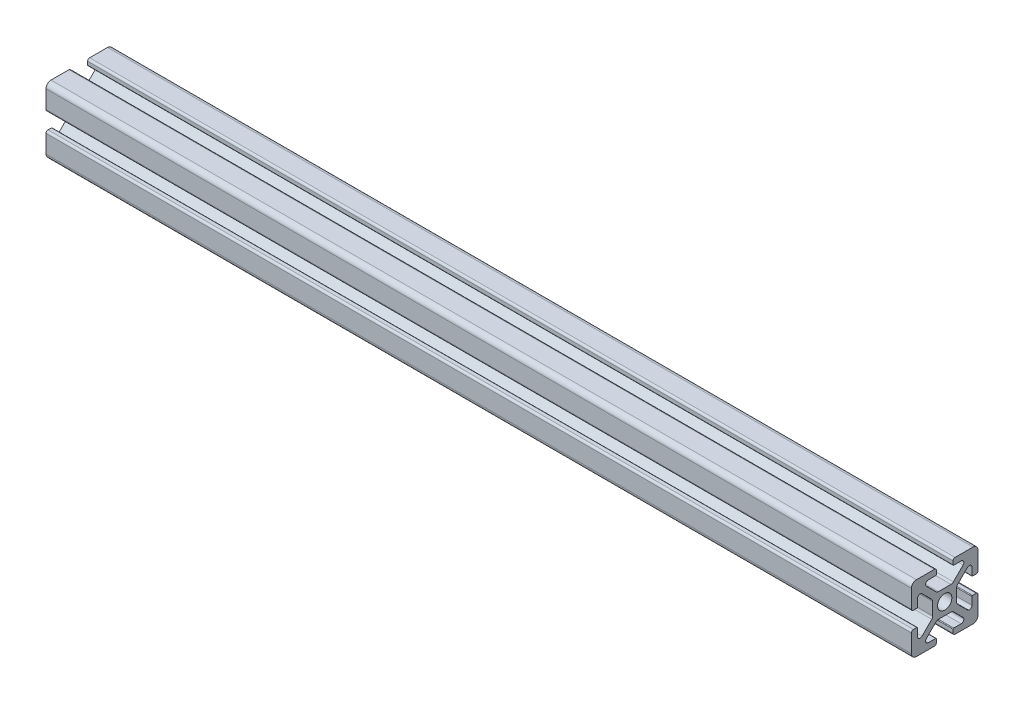
SolidWorks part; units mm, degrees
ref_plane "Front Plane" through (0, 0, 0) normal (0, 0, 1) x (1, 0, 0)
ref_plane "Top Plane" through (0, 0, 0) normal (0, 1, 0) x (1, 0, 0)
ref_plane "Right Plane" through (0, 0, 0) normal (1, 0, 0) x (0, 0, -1)
sketch "Sketch1" plane through (0, 0, 0) normal (1, 0, 0) x (0, 0, -1)
  line L0 (0, -10) -> (0, 10) construction
  line L1 (10, -10) -> (-10, -10)
  line L2 (10, -10) -> (10, 10)
  line L3 (10, 10) -> (0, 10)
  line L4 (-10, -10) -> (-10, 10)
  line L5 (10, -10) -> (-10, 10) construction
  line L6 (10, 10) -> (-10, -10) construction
  line L7 (10, 0) -> (-10, 0) construction
  line L8 (-2.5, 9.4) -> (-2.5, 8.3731)
  line L9 (-2.7, 8.1731) -> (-4.95, 8.1731)
  line L10 (-5.5157, 6.8075) -> (-2.6011, 3.8929)
  line L11 (-1.894, 3.6) -> (0, 3.6)
  line L12 (-5.3502, 4.0584) -> (-4.0584, 5.3502) construction
  line L13 (-3.825, 8.1731) -> (-3.825, 10) construction
  line L14 (-3.1, 10) -> (-10, 10)
  line L15 (-5.75, 7.3731) -> (5.75, 7.3731) construction
  circle A0 centre (0, 0) radius 2.15
  arc A1 (-4.95, 8.1731) -> (-5.5157, 6.8075) centre (-4.95, 7.3731) ccw
  arc A2 (-2.6011, 3.8929) -> (-1.894, 3.6) centre (-1.894, 4.6) ccw
  arc A3 (-2.5, 8.3731) -> (-2.7, 8.1731) centre (-2.7, 8.3731) cw
  arc A4 (-2.5, 9.4) -> (-3.1, 10) centre (-3.1, 9.4) ccw
  point P0 (0, 0)
  point P9 (0, 0)
  point P12 (0, 0)
  point P22 (-4.7043, 4.7043)
  point P32 (-2.5, 10)
  point P33 (-2.5, 8.8866)
  point P35 (-4.0584, 5.3502)
  point P37 (0, 7.3731)
  point P38 (14.0535, 2.7398)
  dimension "Center Hole Diameter" = 4.3
  dimension "D4" = 1
  dimension "D5" = 0.2
  dimension "D6" = 0.6
  dimension "D3" = 0.8
  dimension "Rail Height" = 20
  dimension "D7" = 6.4
  dimension "T Slot Width" = 5
  dimension "D10" = 10
  dimension "Rail Width" = 20
  dimension "D2" = 11.5
sketch "Sketch2" plane through (0, 0, 0) normal (0, 0, 1) x (1, 0, 0)
  line L0 (-132.4, 10) -> (-132.4, -10) construction
  line L1 (152.4, -10) -> (-152.4, -10) construction
  line L2 (152.4, -10) -> (152.4, 10) construction
  line L3 (152.4, 10) -> (-152.4, 10) construction
  line L4 (-152.4, -10) -> (-152.4, 10) construction
  line L5 (152.4, -10) -> (-152.4, 10) construction
  line L6 (152.4, 10) -> (-152.4, -10) construction
  line L7 (132.4, 10) -> (132.4, -10) construction
  point P0 (0, 0)
  point P12 (132.4, 0)
  dimension "Length" = 304.8
  dimension "D1" = 20
  dimension "D2" = 20
sketch "Sketch3" plane through (0, 0, 0) normal (1, 0, 0) x (0, 0, -1)
  line L0 (-5.5157, 6.8075) -> (-2.6011, 3.8929) construction
  line L5 (-3.1, 10) -> (-10, 10) construction
  line L6 (-2.5, 9.4) -> (-2.5, 8.3731) construction
  line L7 (-2.7, 8.1731) -> (-4.95, 8.1731) construction
  line L8 (-1.894, 3.6) -> (0, 3.6) construction
  line L9 (-5.5157, 6.8075) -> (-2.6011, 3.8929)
  line L10 (-10, 10) -> (0, 0) construction
  line L12 (-3.6, 1.894) -> (-3.6, 0)
  line L13 (-8.1731, 2.7) -> (-8.1731, 4.95)
  line L14 (-3.1, 10) -> (-8.5, 10)
  line L15 (-2.5, 9.4) -> (-2.5, 8.3731)
  line L16 (-2.7, 8.1731) -> (-4.95, 8.1731)
  line L17 (-1.894, 3.6) -> (0, 3.6)
  line L18 (-9.4, 2.5) -> (-8.3731, 2.5)
  line L19 (-10, 3.1) -> (-10, 8.5)
  line L20 (-6.8075, 5.5157) -> (-3.8929, 2.6011)
  line L21 (-3.6, 0) -> (-2.15, 0)
  line L22 (0, 3.6) -> (0, 2.15)
  arc A0 (-2.5, 9.4) -> (-3.1, 10) centre (-3.1, 9.4) ccw construction
  arc A1 (-2.7, 8.1731) -> (-2.5, 8.3731) centre (-2.7, 8.3731) ccw construction
  arc A2 (-4.95, 8.1731) -> (-5.5157, 6.8075) centre (-4.95, 7.3731) ccw construction
  arc A3 (-2.6011, 3.8929) -> (-1.894, 3.6) centre (-1.894, 4.6) ccw construction
  arc A4 (-2.5, 9.4) -> (-3.1, 10) centre (-3.1, 9.4) ccw
  arc A5 (-2.7, 8.1731) -> (-2.5, 8.3731) centre (-2.7, 8.3731) ccw
  arc A6 (-4.95, 8.1731) -> (-5.5157, 6.8075) centre (-4.95, 7.3731) ccw
  arc A7 (-2.6011, 3.8929) -> (-1.894, 3.6) centre (-1.894, 4.6) ccw
  arc A8 (-3.8929, 2.6011) -> (-3.6, 1.894) centre (-4.6, 1.894) cw
  arc A9 (-8.1731, 4.95) -> (-6.8075, 5.5157) centre (-7.3731, 4.95) cw
  arc A10 (-8.1731, 2.7) -> (-8.3731, 2.5) centre (-8.3731, 2.7) cw
  arc A11 (-9.4, 2.5) -> (-10, 3.1) centre (-9.4, 3.1) cw
  circle A12 centre (0, 0) radius 2.15 construction
  arc A13 (0, 2.15) -> (-2.15, 0) centre (0, 0) ccw
  arc A14 (-10, 8.5) -> (-8.5, 10) centre (-8.5, 8.5) cw
  dimension "D1" = 1.5
extrude "Boss-Extrude1" add sketch "Sketch3" against normal blind 260
mirror "Mirror1" about plane through (0, 0, 0) normal (0, 1, 0) of bodies 104
mirror "Mirror2" about plane through (0, 0, 0) normal (0, 0, 1) of bodies 105
equation "\"D10@Sketch1\" = \"Rail Height@Sketch1\" / 2"
equation "\"D2@Sketch2\"=\"D1@Sketch2\""
